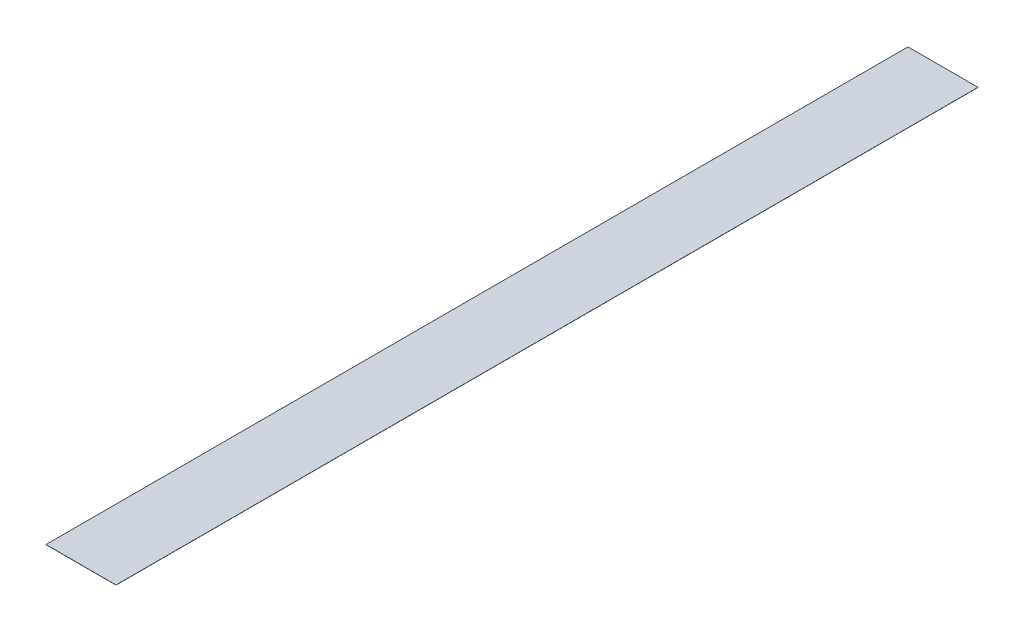
SolidWorks part; units mm, degrees
material "acrylic adhesive"
ref_plane "Front" through (0, 0, 0) normal (0, 0, 1) x (1, 0, 0)
ref_plane "Top" through (0, 0, 0) normal (0, 1, 0) x (1, 0, 0)
ref_plane "Right" through (0, 0, 0) normal (1, 0, 0) x (0, 0, -1)
sketch "Sketch1" plane through (0, 0, 0) normal (0, 1, 0) x (1, 0, 0)
  line L0 (12.45, 153.25) -> (-12.45, -153.25) construction
  line L1 (-12.45, 153.25) -> (12.45, 153.25)
  line L2 (-12.45, 153.25) -> (-12.45, -153.25)
  line L3 (-12.45, -153.25) -> (12.45, -153.25)
  line L4 (12.45, 153.25) -> (12.45, -153.25)
  point P4 (0, 0)
  dimension "D1" = 306.5
  dimension "D2" = 24.9
extrude "Extrude1" add sketch "Sketch1" along normal blind 0.0508
